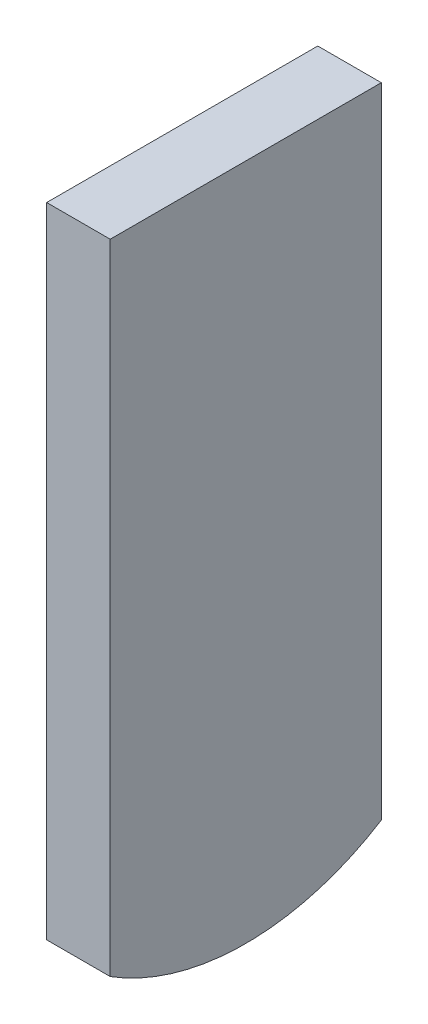
SolidWorks part; units mm, degrees
material "AISI 304"
ref_plane "前视基准面" through (0, 0, 0) normal (0, 0, 1) x (1, 0, 0)
ref_plane "上视基准面" through (0, 0, 0) normal (0, 1, 0) x (1, 0, 0)
ref_plane "右视基准面" through (0, 0, 0) normal (1, 0, 0) x (0, 0, -1)
ref_plane "ConnectFace" through (0, 0, 0) normal (0, 1, 0) x (1, 0, 0)
ref_plane "CenterV" through (0, 0, 0) normal (1, 0, 0) x (0, 0, -1)
ref_plane "CenterH" through (0, 0, 0) normal (0, 0, 1) x (1, 0, 0)
sketch "SPin" plane through (0, 0, 0) normal (0, 1, 0) x (1, 0, 0)
  line L1 (-0.75, -3.2) -> (0.75, -3.2)
  line L2 (-0.75, -3.2) -> (-0.75, 3.2)
  line L3 (-0.75, 3.2) -> (0.75, 3.2)
  line L4 (0.75, -3.2) -> (0.75, 3.2)
  line L5 (-0.75, -3.2) -> (0.75, 3.2) construction
  line L6 (-0.75, 3.2) -> (0.75, -3.2) construction
  point P0 (0, 0)
  dimension "b" = 6.4
  dimension "t" = 1.5
extrude "FPin" add sketch "SPin" against normal blind 16
sketch "SPin2" plane through (0, 0, 0) normal (1, 0, 0) x (0, 0, -1)
  line L0 (0, 0) -> (0, -16) construction
  arc A0 (-3.2, -15.0754) -> (3.2, -15.0754) centre (0, -10) ccw
  dimension "R" = 6
  dimension "D1" = 16
  dimension "D2" = 6.4
extrude "FPin2" cut sketch "SPin2" against normal through all and the other way through all flip side to cut
sketch "CircleBase" plane through (0, 0, 0) normal (0, 1, 0) x (1, 0, 0)
  circle A0 centre (0, 0) radius 5
  dimension "D1" = 10
sketch "RectangleBase" plane through (0, 0, 0) normal (0, 1, 0) x (1, 0, 0)
  line L0 (1.75, 4.2) -> (-1.75, 4.2)
  line L1 (-1.75, 4.2) -> (-1.75, -4.2)
  line L2 (-1.75, -4.2) -> (1.75, -4.2)
  line L3 (1.75, -4.2) -> (1.75, 4.2)
  line L4 (-0.75, -3.2) -> (0.75, -3.2)
  line L5 (0.75, -3.2) -> (0.75, 3.2)
  line L6 (0.75, 3.2) -> (-0.75, 3.2)
  line L7 (-0.75, 3.2) -> (-0.75, -3.2)
  line L8 (-0.75, -3.2) -> (0.75, -3.2) construction
  line L9 (0.75, -3.2) -> (0.75, 3.2) construction
  line L10 (0.75, 3.2) -> (-0.75, 3.2) construction
  line L11 (-0.75, 3.2) -> (-0.75, -3.2) construction
  dimension "D1" = 0
  dimension "D2" = 1
equation "\"D1@SPin2\"=\"L@FPin\""
equation "\"D2@SPin2\"=\"b@SPin\""
